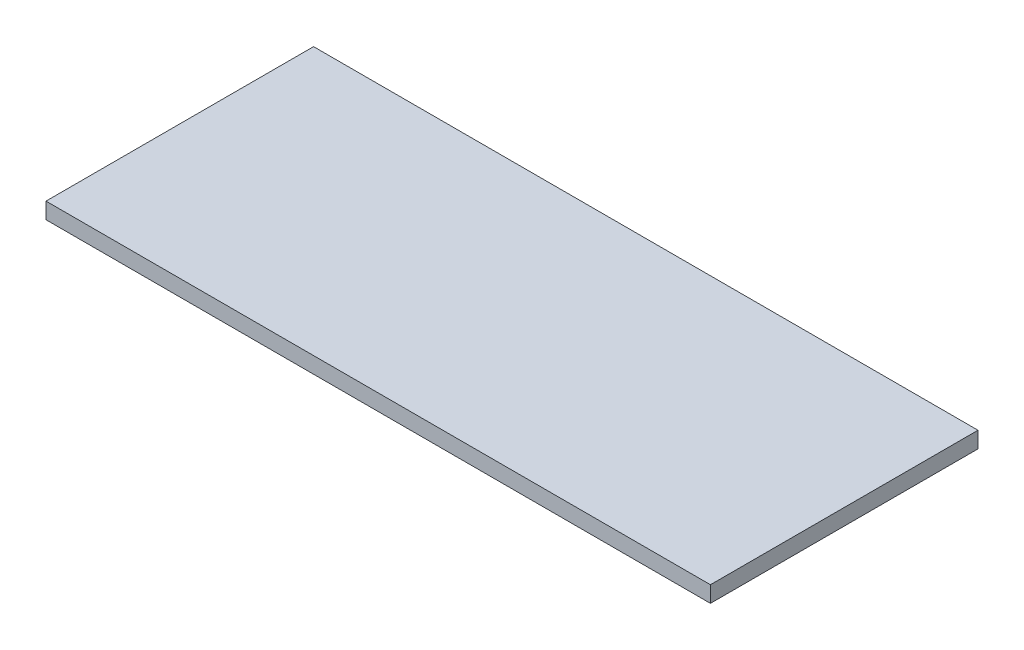
SolidWorks part; units mm, degrees
ref_plane "Спереди" through (0, 0, 0) normal (0, 0, 1) x (1, 0, 0)
ref_plane "Сверху" through (0, 0, 0) normal (0, 1, 0) x (1, 0, 0)
ref_plane "Справа" through (0, 0, 0) normal (1, 0, 0) x (0, 0, -1)
sketch "Эскиз1" plane through (0, 0, 0) normal (0, 1, 0) x (1, 0, 0)
  line L1 (370, -149) -> (-370, -149)
  line L2 (370, -149) -> (370, 149)
  line L3 (370, 149) -> (-370, 149)
  line L4 (-370, -149) -> (-370, 149)
  line L5 (370, -149) -> (-370, 149) construction
  line L6 (370, 149) -> (-370, -149) construction
  point P0 (0, 0)
  dimension "D1" = 740
  dimension "D2" = 298
extrude "Бобышка-Вытянуть1" add sketch "Эскиз1" along normal blind 18
